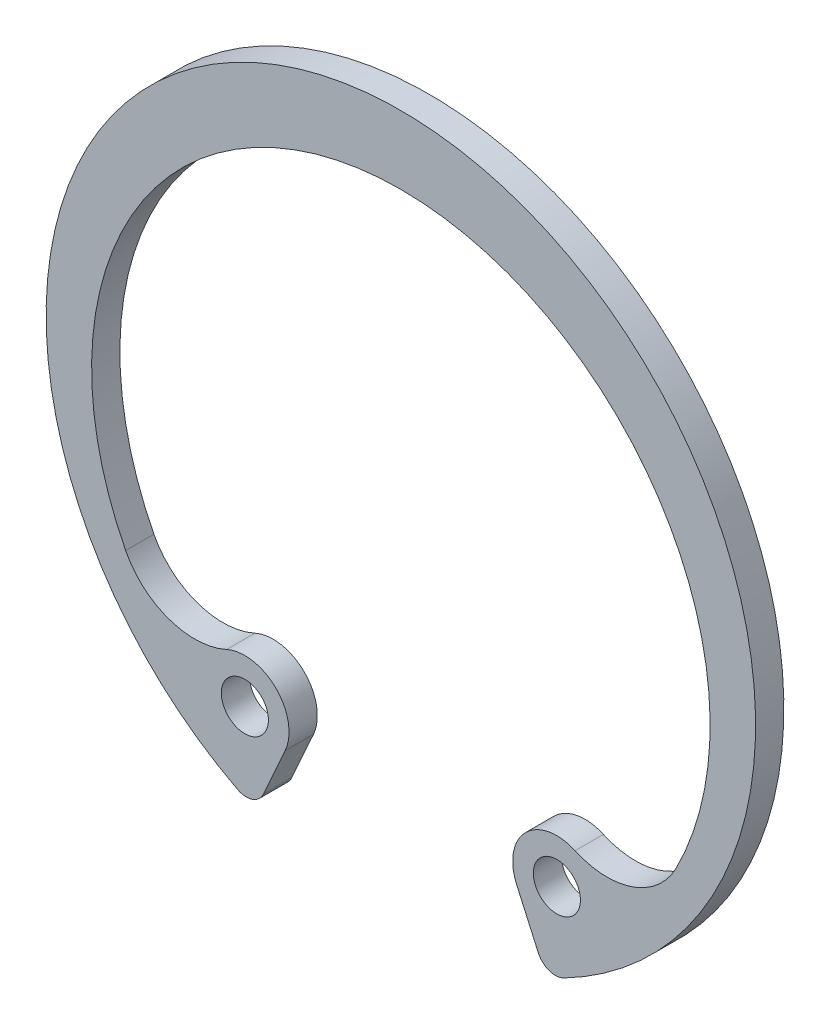
SolidWorks part; units mm, degrees
ref_plane "Front Plane" through (0, 0, 0) normal (0, 0, 1) x (1, 0, 0)
ref_plane "Top Plane" through (0, 0, 0) normal (0, 1, 0) x (1, 0, 0)
ref_plane "Right Plane" through (0, 0, 0) normal (1, 0, 0) x (0, 0, -1)
sketch "Sketch1" plane through (0, 0, 0) normal (0, 0, 1) x (1, 0, 0)
  line L0 (0, 15.05) -> (0, 12.15) construction
  line L1 (-15.05, 0) -> (-13.6, 0) construction
  line L2 (0, 0) -> (0, -15.05) construction
  line L3 (-4.2, -9.35) -> (-6.1668, -13.7285) construction
  line L4 (-4.2, -9.35) -> (-6.2, -9.35) construction
  circle A0 centre (0, 0) radius 14.7 construction
  circle A1 centre (0, 0) radius 15.05 construction
  circle A2 centre (0, 0) radius 14 construction
  dimension "Ring OD" = 30.1
  dimension "For ID" = 28
  dimension "Maximum Section" = 2.9
  dimension "Minimum Section" = 1.45
  dimension "Gap Width" = 8.4
  dimension "Lug Height" = 4.8
  dimension "Hole Diameter" = 2
sketch "Sketch2" plane through (0, 0, 0) normal (1, 0, 0) x (0, 0, -1)
  line L0 (-0.65, 15.05) -> (0.65, 15.05) construction
  line L1 (-0.6, -15.05) -> (0.6, -15.05) construction
  point P3 (0, 15.05)
  point P7 (0, -15.05)
  point P8 (-0.6, -15.05)
  point P10 (0.6, -15.05)
  point P11 (-0.65, 15.05)
  point P12 (0.65, 15.05)
  dimension "For Groove Width" = 1.3
  dimension "Ring Thickness" = 1.2
sketch "Sketch3" plane through (0, 0, 0) normal (0, 0, 1) x (1, 0, 0)
  line L0 (-6.1668, -13.7285) -> (-4.2511, -9.4638) construction
  line L1 (-4.2511, -9.4638) -> (-6.8166, -7.7924) construction
  line L2 (0, 0) -> (-5.5954, -8.588) construction
  line L3 (-11.6758, -6.9568) -> (0, 0) construction
  line L4 (0, 0) -> (0, -15.05) construction
  line L5 (-6.8166, -7.7924) -> (0, 0) construction
  line L6 (-5.5954, -8.588) -> (-6.6189, -10.159) construction
  line L7 (-6.6189, -10.159) -> (-7.6424, -11.73) construction
  line L8 (0, 15.05) -> (0, 12.15) construction
  line L11 (-4.9085, -10.9273) -> (-6.1668, -13.7285)
  line L12 (0, 0) -> (0, -15.05) construction
  line L13 (4.9085, -10.9273) -> (6.1668, -13.7285)
  line L14 (-4.2, -9.35) -> (-6.1668, -13.7285) construction
  line L15 (-5.5954, -8.588) -> (-8.2156, -12.6098) construction
  arc A0 (-6.1668, -13.7285) -> (6.1668, -13.7285) centre (0, 0) cw
  circle A1 centre (0, 0) radius 15.05 construction
  arc A2 (-11.6758, -6.9568) -> (11.6758, -6.9568) centre (0, -0.9708) cw
  circle A4 centre (-6.6189, -10.159) radius 1
  circle A5 centre (0, 0) radius 13.6 construction
  circle A7 centre (6.6189, -10.159) radius 1
  circle A8 centre (0, 0) radius 14 construction
  arc A9 (-7.393, -8.4513) -> (-4.9085, -10.9273) centre (-6.6189, -10.159) cw
  arc A10 (-11.6758, -6.9568) -> (-7.393, -8.4513) centre (-8.7503, -5.457) ccw
  arc A11 (7.393, -8.4513) -> (4.9085, -10.9273) centre (6.6189, -10.159) ccw
  arc A12 (11.6758, -6.9568) -> (7.393, -8.4513) centre (8.7503, -5.457) cw
  point P3 (0, -15.05)
  dimension "D1" = 2
  dimension "D2" = 4.8
  dimension "D3" = 7.8
extrude "Boss-Extrude1" add sketch "Sketch3" against normal up to vertex (0.6 mm away) and the other way up to vertex (0.6 mm away) up to point (0, -15.05, -0.6) other way up to point (0, -15.05, 0.6)
fillet "Fillet1" radius 0.7937 2 edges at (6.1668, -13.7285, 0) (-6.1668, -13.7285, 0)
equation "\"D1@Sketch3\"=\"Hole Diameter@Sketch1\""
equation "\"Minimum Section@Sketch1\"=\"Maximum Section@Sketch1\"*.5"
equation "\"Gap Width@Sketch1\"=\"For ID@Sketch1\"*.3"
equation "\"D2@Sketch3\"=\"Lug Height@Sketch1\""
equation "\"D3@Sketch3\"=\"Lug Height@Sketch1\"*1.625"
